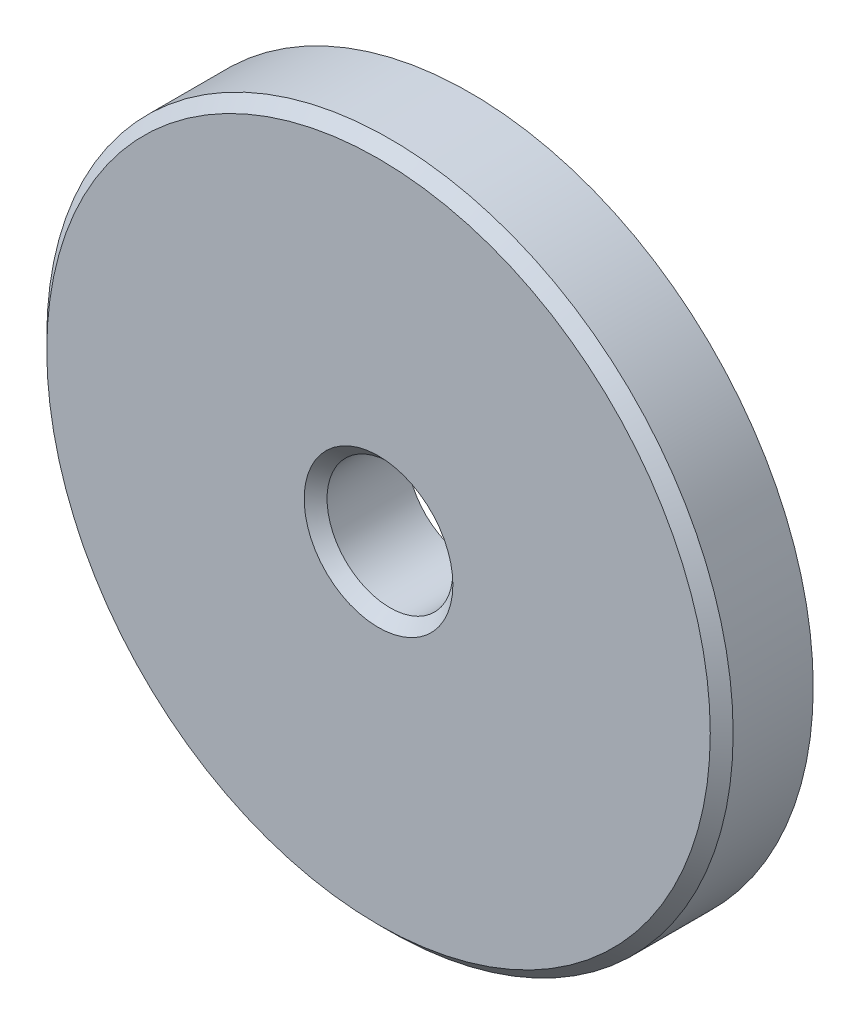
SolidWorks part; units mm, degrees
material "普通碳钢"
ref_plane "前视基准面" through (0, 0, 0) normal (0, 0, 1) x (1, 0, 0)
ref_plane "上视基准面" through (0, 0, 0) normal (0, 1, 0) x (1, 0, 0)
ref_plane "右视基准面" through (0, 0, 0) normal (1, 0, 0) x (0, 0, -1)
sketch "草图1" plane through (0, 0, 0) normal (0, 0, 1) x (1, 0, 0)
  circle A0 centre (0, 0) radius 15
  circle A1 centre (0, 0) radius 2.75
  dimension "D1" = 30
  dimension "D2" = 5.5
extrude "凸台-拉伸1" add sketch "草图1" along normal blind 4
chamfer "倒角1" distance 0.5 angle 45 2 edges at (2.75, 0, 4) (15, 0, 4)
